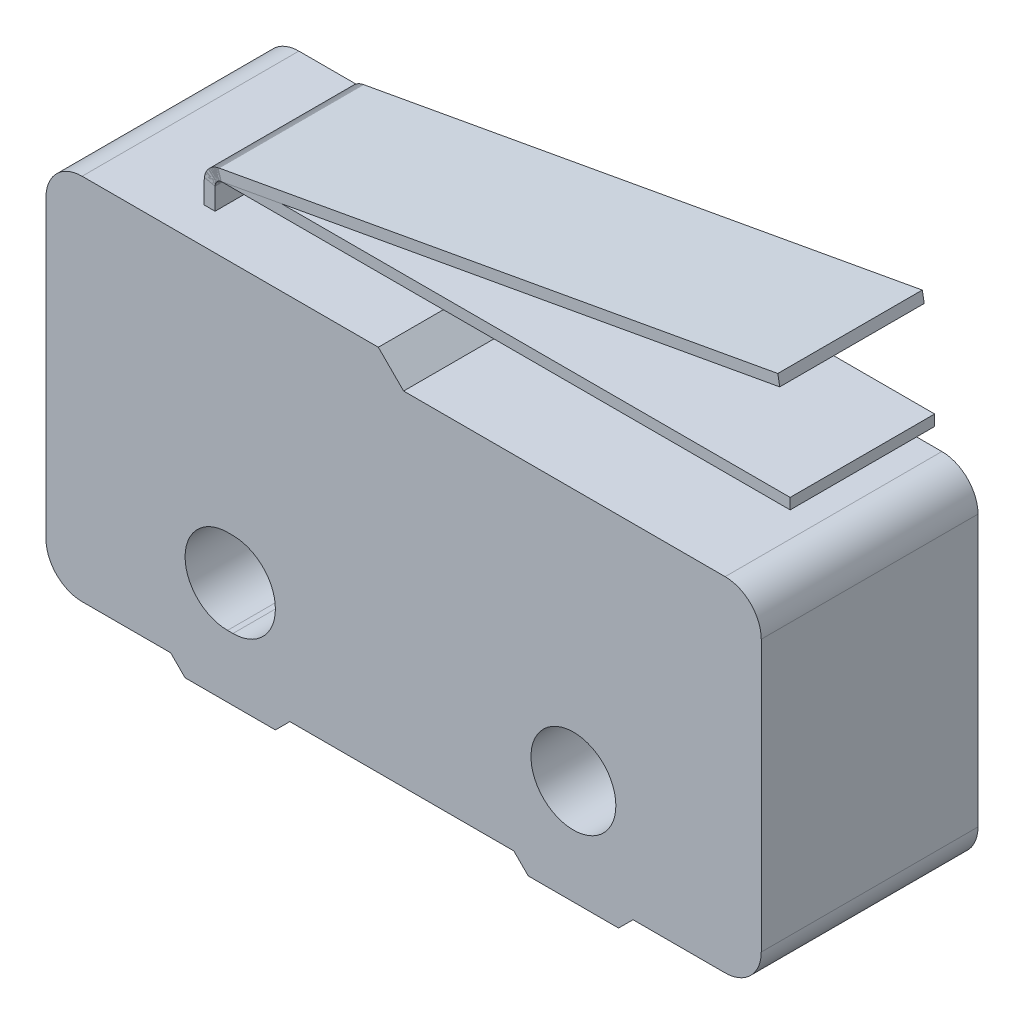
SolidWorks part; units mm, degrees
ref_plane "Front Plane" through (0, 0, 0) normal (0, 0, 1) x (1, 0, 0)
ref_plane "Top Plane" through (0, 0, 0) normal (0, 1, 0) x (1, 0, 0)
ref_plane "Right Plane" through (0, 0, 0) normal (1, 0, 0) x (0, 0, -1)
sketch "Sketch1" plane through (0, 0, 0) normal (0, 0, 1) x (1, 0, 0)
  line L0 (-9.9, -5.1) -> (-9.9, 5.1)
  line L1 (-9.9, 5.1) -> (-0.7, 5.1)
  line L2 (-0.7, 5.1) -> (0, 4.4)
  line L3 (0, 4.4) -> (9.9, 4.4)
  line L4 (9.9, 4.4) -> (9.9, -5.1)
  line L5 (-4.875, -2.6) -> (-4.725, -2.6) construction
  line L6 (9.9, -5.1) -> (6.35, -5.1)
  line L7 (-4.875, -1.425) -> (-4.725, -1.425)
  line L8 (-4.875, -3.775) -> (-4.725, -3.775)
  line L9 (-6.45, -5.1) -> (-6.05, -5.5)
  line L10 (-6.05, -5.5) -> (-3.55, -5.5)
  line L11 (-3.55, -5.5) -> (-3.15, -5.1)
  line L12 (-4.8, -5.5) -> (-4.8, -2.6) construction
  line L13 (-0.05, -1.425) -> (-0.05, -3.775) construction
  line L14 (3.45, -5.5) -> (3.05, -5.1)
  line L15 (5.95, -5.5) -> (3.45, -5.5)
  line L16 (6.35, -5.1) -> (5.95, -5.5)
  line L17 (3.05, -5.1) -> (-3.15, -5.1)
  line L18 (-6.45, -5.1) -> (-9.9, -5.1)
  line L19 (-9.9, 0) -> (9.9, 0) construction
  arc A0 (-4.875, -1.425) -> (-4.875, -3.775) centre (-4.875, -2.6) ccw
  circle A1 centre (4.7, -2.6) radius 1.175
  arc A2 (-4.725, -3.775) -> (-4.725, -1.425) centre (-4.725, -2.6) ccw
  point P8 (-9.9, 0)
  point P14 (-4.8, -2.6)
  point P21 (-4.8, -5.5)
  dimension "D6" = 2.35
  dimension "D7" = 2.35
  dimension "D8" = 2.5
  dimension "D1" = 9.5
  dimension "D2" = 10.2
  dimension "D3" = 19.8
  dimension "D4" = 0.7
  dimension "D5" = 9.9
  dimension "D9" = 9.5
  dimension "D10" = 2.5
  dimension "D11" = 5.2
  dimension "D12" = 2.9
  dimension "D13" = 2.5
extrude "Boss-Extrude1" add sketch "Sketch1" along normal mid plane 6
fillet "Fillet1" radius 1 4 edges at (9.9, -5.1, 0) (-9.9, -5.1, 0) (-9.9, 5.1, 0) (9.9, 4.4, 0)
sketch "Sketch2" plane through (0, 0, 0) normal (0, 0, 1) x (1, 0, 0)
  line L0 (-6.52, 5.1) -> (-6.52, 5.7)
  line L1 (-0.7, 5.1) -> (-8.9, 5.1) construction
  line L2 (-6.02, 6.2) -> (9.7, 6.2)
  line L3 (-4.725, -1.425) -> (-4.875, -1.425) construction
  line L4 (-9.9, 4.1) -> (-9.9, -4.1) construction
  line L5 (-6.22, 5.1) -> (-6.22, 5.7)
  line L6 (-6.02, 5.9) -> (9.7, 5.9)
  line L7 (-6.22, 5.1) -> (-6.52, 5.1)
  line L8 (9.7, 6.2) -> (9.7, 5.9)
  arc A0 (-6.52, 5.7) -> (-6.02, 6.2) centre (-6.02, 5.7) cw
  arc A1 (-4.875, -1.425) -> (-4.875, -3.775) centre (-4.875, -2.6) ccw construction
  circle A2 centre (4.7, -2.6) radius 1.175 construction
  arc A3 (-6.22, 5.7) -> (-6.02, 5.9) centre (-6.02, 5.7) cw
  point P6 (-4.8, -2.6)
  point P10 (-4.8, -1.425)
  point P14 (-6.05, -2.6)
  dimension "D1" = 14.5
  dimension "D3" = 8.8
  dimension "D4" = 0.5
  dimension "D2" = 3.38
  dimension "D5" = 0.3
extrude "Boss-Extrude3" add sketch "Sketch2" along normal mid plane 4
sketch "Sketch4" plane through (0, 0, 0) normal (0, 0, 1) x (1, 0, 0)
  line L0 (-6.52, 5.1) -> (-6.52, 5.7)
  line L1 (-6.1093, 6.192) -> (9.3579, 9)
  line L2 (9.7, 6.2) -> (-6.02, 6.2) construction
  line L3 (-6.22, 5.1) -> (-6.22, 5.7)
  line L4 (-6.0557, 5.8968) -> (9.4114, 8.7048)
  line L5 (9.4114, 8.7048) -> (9.3579, 9)
  line L6 (-6.52, 5.1) -> (-6.22, 5.1)
  arc A0 (-6.52, 5.7) -> (-6.1093, 6.192) centre (-6.02, 5.7) cw
  arc A1 (-6.02, 6.2) -> (-6.52, 5.7) centre (-6.02, 5.7) ccw construction
  arc A2 (-6.22, 5.7) -> (-6.0557, 5.8968) centre (-6.02, 5.7) cw
  dimension "D1" = 2.8
  dimension "D2" = 0.3
extrude "Boss-Extrude4" add sketch "Sketch4" along normal mid plane 4 separate body
